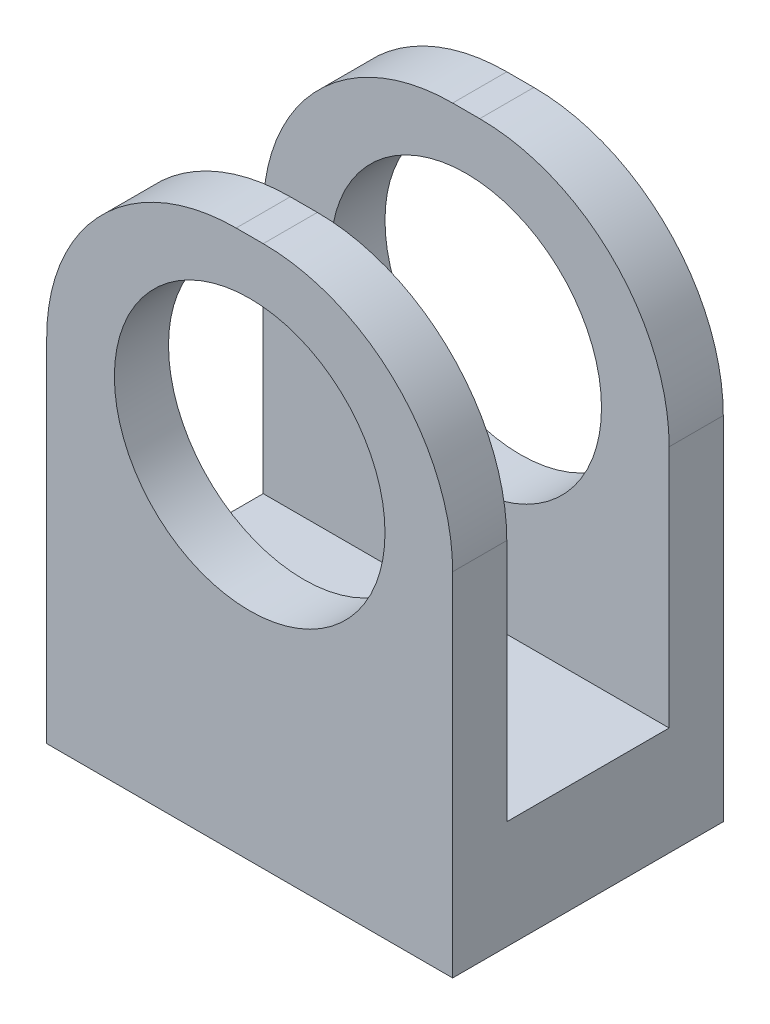
SolidWorks part; units mm, degrees
ref_plane "Alzado" through (0, 0, 0) normal (0, 0, 1) x (1, 0, 0)
ref_plane "Planta" through (0, 0, 0) normal (0, 1, 0) x (1, 0, 0)
ref_plane "Vista lateral" through (0, 0, 0) normal (1, 0, 0) x (0, 0, -1)
sketch "Croquis1" plane through (0, 0, 0) normal (0, 0, 1) x (1, 0, 0)
  line L1 (-3.8525, 10.4855) -> (-2.8525, 10.4855)
  line L2 (-10.8525, 3.4855) -> (-10.8525, -9.5145)
  line L3 (-10.8525, -9.5145) -> (4.1475, -9.5145)
  line L4 (4.1475, 3.4855) -> (4.1475, -9.5145)
  arc A0 (-10.8525, 3.4855) -> (-3.8525, 10.4855) centre (-3.8525, 3.4855) cw
  arc A1 (4.1475, 3.4855) -> (-2.8525, 10.4855) centre (-2.8525, 3.4855) ccw
  circle A2 centre (-3.3525, 3.4855) radius 5
  point P6 (-10.8525, 10.4855)
  point P9 (4.1475, 10.4855)
  dimension "D3" = 7
  dimension "D4" = 7
  dimension "D5" = 10
  dimension "D1" = 20
  dimension "D2" = 15
  dimension "D6" = 7.5
  dimension "D7" = 7
extrude "Saliente-Extruir1" add sketch "Croquis1" along normal blind 10
sketch "Croquis2" plane through (4.1475, 0, 0) normal (1, 0, 0) x (0, 0, -1)
  line L0 (-10, 10.4855) -> (0, 10.4855) construction
  line L1 (-8, 10.4855) -> (-2, 10.4855)
  line L2 (-8, 10.4855) -> (-8, -5.5145)
  line L3 (-8, -5.5145) -> (-2, -5.5145)
  line L4 (-2, 10.4855) -> (-2, -5.5145)
  line L5 (-10, -9.5145) -> (-10, 3.4855) construction
  line L6 (0, -9.5145) -> (0, 3.4855) construction
  dimension "D1" = 2
  dimension "D2" = 2
  dimension "D3" = 16
extrude "Cortar-Extruir1" cut sketch "Croquis2" against normal through all
